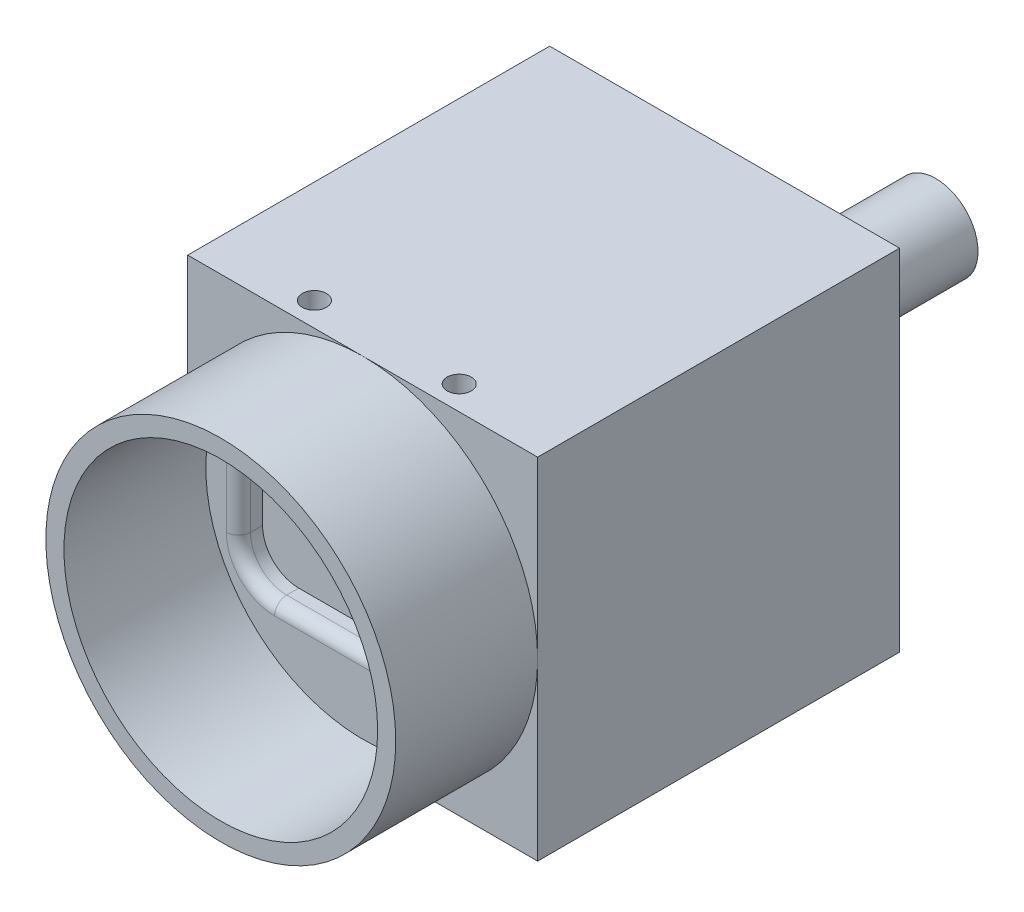
SolidWorks part; units mm, degrees
ref_plane "Front Plane" through (0, 0, 0) normal (0, 0, 1) x (1, 0, 0)
ref_plane "Top Plane" through (0, 0, 0) normal (0, 1, 0) x (1, 0, 0)
ref_plane "Right Plane" through (0, 0, 0) normal (1, 0, 0) x (0, 0, -1)
sketch "Sketch1" plane through (0, 0, 0) normal (0, 0, 1) x (1, 0, 0)
  line L1 (-15.2805, 10.5567) -> (13.7195, 10.5567)
  line L2 (-15.2805, 10.5567) -> (-15.2805, -18.4433)
  line L3 (-15.2805, -18.4433) -> (13.7195, -18.4433)
  line L4 (13.7195, 10.5567) -> (13.7195, -18.4433)
  dimension "D1" = 29
  dimension "D2" = 29
extrude "Boss-Extrude1" add sketch "Sketch1" along normal blind 30 contours L1 L4 L3 L2
sketch "Sketch2" plane through (0, 0, 30) normal (0, 0, 1) x (1, 0, 0)
  line L0 (-15.2805, 10.5567) -> (13.7195, 10.5567) construction
  circle A0 centre (-0.7805, -3.9433) radius 14.5
  circle A1 centre (-0.7805, -3.9433) radius 13
  dimension "D2" = 29
  dimension "D3" = 26
  dimension "D1" = 14.5
extrude "Boss-Extrude2" add sketch "Sketch2" along normal blind 11.76
sketch "Sketch4" plane through (0, 0, 30) normal (0, 0, 1) x (1, 0, 0)
  line L0 (-0.7805, 10.5567) -> (-0.7805, -18.4433) construction
  line L1 (-11.0805, 2.8567) -> (9.5195, 2.8567)
  line L2 (-11.0805, 2.8567) -> (-11.0805, -10.7433)
  line L3 (-11.0805, -10.7433) -> (9.5195, -10.7433)
  line L4 (9.5195, 2.8567) -> (9.5195, -10.7433)
  line L5 (-15.2805, -3.9433) -> (13.7195, -3.9433) construction
  dimension "D1" = 6.8
  dimension "D2" = 10.3
  dimension "D3" = 6.8
  dimension "D4" = 10.3
extrude "Cut-Extrude1" cut sketch "Sketch4" against normal blind 2
fillet "Fillet1" radius 3 4 edges at (-11.0805, -10.7433, 29) (9.5195, -10.7433, 29) (9.5195, 2.8567, 29) (-11.0805, 2.8567, 29)
fillet "Fillet2" radius 1 8 edges at (-10.2018, 1.978, 30) (-0.7805, 2.8567, 30) (8.6409, 1.978, 30) (9.5195, -3.9433, 30) (8.6409, -9.8647, 30) (-0.7805, -10.7433, 30) (-10.2018, -9.8647, 30) (-11.0805, -3.9433, 30)
sketch "Sketch5" plane through (0, 0, 0) normal (0, 0, -1) x (-1, 0, 0)
  line L0 (15.2805, 10.5567) -> (-13.7195, 10.5567) construction
  line L1 (-13.7195, 10.5567) -> (-13.7195, -18.4433) construction
  circle A0 centre (-8.7195, 5.5567) radius 3.5
  circle A1 centre (-8.7195, 5.5567) radius 2.5
  dimension "D3" = 5
  dimension "D5" = 7
  dimension "D1" = 5
  dimension "D2" = 5
extrude "Boss-Extrude3" add sketch "Sketch5" along normal blind 8 contours A0
sketch "Sketch6" plane through (0, 10.5567, 0) normal (0, 1, 0) x (1, 0, 0)
  line L0 (-0.7805, 0) -> (-0.7805, -30) construction
  line L1 (-15.2805, 0) -> (13.7195, 0) construction
  line L2 (-15.2805, -30) -> (-0.7805, -30) construction
  circle A0 centre (-6.7805, -28) radius 1
  circle A1 centre (5.2195, -28) radius 1
  dimension "D1" = 6
  dimension "D3" = 2
extrude "Cut-Extrude2" cut sketch "Sketch6" against normal blind 3
sketch "Sketch8" plane through (0, -18.4433, 0) normal (0, -1, 0) x (1, 0, 0)
  line L0 (-0.7805, 30) -> (13.7195, 30) construction
  line L1 (-0.7805, 0) -> (-0.7805, 30) construction
  line L2 (-15.2805, 0) -> (13.7195, 0) construction
  line L3 (-15.2805, 30) -> (-0.7805, 30) construction
  line L5 (-12.2805, 22.2926) -> (10.7195, 22.2926)
  line L6 (-13.2805, 21.2926) -> (-13.2805, 7.2926)
  line L7 (-12.2805, 6.2926) -> (10.7195, 6.2926)
  line L8 (11.7195, 21.2926) -> (11.7195, 7.2926)
  circle A0 centre (9.2195, 27) radius 1.5
  circle A1 centre (-10.7805, 27) radius 1.5
  circle A2 centre (-6.7805, 25.5) radius 1
  circle A3 centre (5.2195, 25.5) radius 1
  circle A4 centre (-6.7805, 3.5) radius 1
  circle A5 centre (5.2195, 3.5) radius 1
  circle A6 centre (-0.7805, 3.5) radius 1.5
  arc A7 (10.7195, 22.2926) -> (11.7195, 21.2926) centre (10.7195, 21.2926) cw
  arc A8 (11.7195, 7.2926) -> (10.7195, 6.2926) centre (10.7195, 7.2926) cw
  arc A9 (-13.2805, 7.2926) -> (-12.2805, 6.2926) centre (-12.2805, 7.2926) ccw
  arc A10 (-12.2805, 22.2926) -> (-13.2805, 21.2926) centre (-12.2805, 21.2926) ccw
  dimension "D1" = 3
  dimension "D4" = 4.5
  dimension "D5" = 12
  dimension "D6" = 22
  dimension "D7" = 12.5
  dimension "D10" = 1
  dimension "D2" = 3
  dimension "D3" = 20
  dimension "D8" = 12.5
  dimension "D9" = 16
extrude "Cut-Extrude3" cut sketch "Sketch8" against normal blind 2
sketch "Sketch9" plane through (0, 0, 0) normal (0, 0, -1) x (-1, 0, 0)
  line L0 (15.2805, -18.4433) -> (-13.7195, -18.4433) construction
  line L1 (-9.7195, -16.4433) -> (12.2805, -16.4433)
  line L2 (-9.7195, -16.4433) -> (-9.7195, -10.4433)
  line L3 (-9.7195, -10.4433) -> (12.2805, -10.4433)
  line L4 (12.2805, -16.4433) -> (12.2805, -10.4433)
  line L5 (15.2805, 10.5567) -> (15.2805, -18.4433) construction
  dimension "D1" = 22
  dimension "D2" = 6
  dimension "D3" = 2
  dimension "D4" = 3
extrude "Boss-Extrude4" add sketch "Sketch9" along normal blind 1 contours L1 L4 L3 L2
sketch "Sketch10" plane through (0, 0, -1) normal (0, 0, -1) x (-1, 0, 0)
  line L0 (12.2805, -16.4433) -> (12.2805, -10.4433) construction
  line L1 (-9.7195, -10.4433) -> (12.2805, -10.4433) construction
  circle A0 centre (-7.7195, -13.4433) radius 1
  circle A1 centre (10.2805, -13.4433) radius 1
  point P4 (0, 0)
  point P5 (0, 0)
  point P10 (0, 0)
  dimension "D1" = 2
  dimension "D2" = 2
  dimension "D3" = 18
  dimension "D4" = 2
  dimension "D5" = 3
  dimension "D6" = 3
extrude "Cut-Extrude4" cut sketch "Sketch10" against normal blind 2
